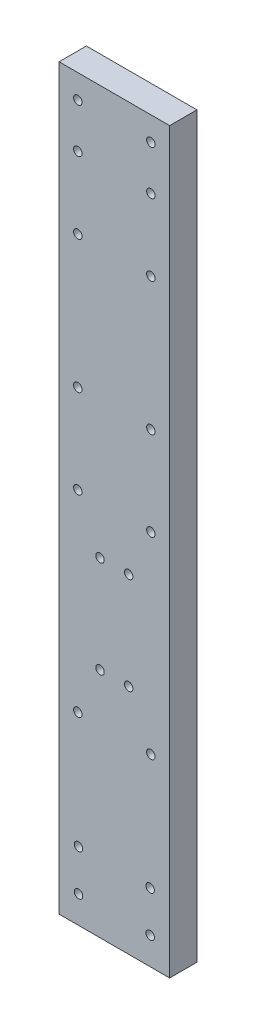
SolidWorks part; units mm, degrees
ref_plane "Front Plane" through (0, 0, 0) normal (0, 0, 1) x (1, 0, 0)
ref_plane "Top Plane" through (0, 0, 0) normal (0, 1, 0) x (1, 0, 0)
ref_plane "Right Plane" through (0, 0, 0) normal (1, 0, 0) x (0, 0, -1)
sketch "Sketch1" plane through (0, 0, 0) normal (0, 0, 1) x (1, 0, 0)
  line L0 (16.2, 0) -> (16.2, 108.14)
  line L1 (16.2, 108.14) -> (0, 108.14)
  line L2 (0, 108.14) -> (0, 0)
  line L3 (0, 0) -> (16.2, 0)
  line L4 (16.2, 57.71) -> (0, 57.71) construction
  line L5 (0, 12.5) -> (16.2, 12.5) construction
  line L6 (0, 24.5) -> (16.2, 24.5) construction
  line L7 (0, 90.16) -> (16.2, 90.16) construction
  line L8 (0, 65.71) -> (16.2, 65.71) construction
  line L9 (8.1, 108.14) -> (8.1, 96.16) construction
  line L11 (0, 96.16) -> (16.2, 96.16) construction
  circle A0 centre (13.45, 55.21) radius 0.62
  circle A1 centre (10.2, 48.21) radius 0.62
  circle A2 centre (13.45, 104.66) radius 0.62
  circle A3 centre (2.75, 98.16) radius 0.62
  circle A4 centre (6, 48.21) radius 0.62
  circle A5 centre (2.75, 27) radius 0.62
  circle A6 centre (2.75, 87.66) radius 0.62
  circle A7 centre (2.75, 55.21) radius 0.62
  circle A8 centre (13.45, 87.66) radius 0.62
  circle A9 centre (13.45, 98.16) radius 0.62
  circle A28 centre (13.45, 68.21) radius 0.62
  circle A29 centre (6, 34) radius 0.62
  circle A32 centre (2.75, 104.66) radius 0.62
  circle A33 centre (10.2, 34) radius 0.62
  circle A34 centre (2.75, 68.21) radius 0.62
  circle A35 centre (13.45, 27) radius 0.62
  circle A36 centre (2.85, 10) radius 0.62
  circle A37 centre (13.35, 10) radius 0.62
  circle A38 centre (13.35, 4) radius 0.62
  circle A39 centre (2.85, 4) radius 0.62
  dimension "D1" = 4
  dimension "D45" = 1.24
  dimension "D2" = 4
  dimension "D3" = 2.85
  dimension "D4" = 2.85
  dimension "D5" = 16.2
  dimension "D6" = 6
  dimension "D7" = 6
  dimension "D8" = 2.85
  dimension "D9" = 2.85
  dimension "D10" = 2.5
  dimension "D11" = 12
  dimension "D12" = 33.21
  dimension "D13" = 2.5
  dimension "D14" = 2.5
  dimension "D15" = 2.75
  dimension "D16" = 2.75
  dimension "D17" = 2.5
  dimension "D18" = 2.5
  dimension "D19" = 2.75
  dimension "D20" = 2.75
  dimension "D21" = 9.5
  dimension "D22" = 6
  dimension "D23" = 9.5
  dimension "D24" = 6
  dimension "D25" = 9.5
  dimension "D26" = 9.5
  dimension "D27" = 6
  dimension "D28" = 6
  dimension "D29" = 8
  dimension "D30" = 24.45
  dimension "D31" = 2.5
  dimension "D32" = 2.5
  dimension "D33" = 2.75
  dimension "D34" = 2.75
  dimension "D35" = 6
  dimension "D36" = 2.75
  dimension "D37" = 2
  dimension "D38" = 2.75
  dimension "D39" = 8.5
  dimension "D40" = 11.98
  dimension "D41" = 2.5
  dimension "D42" = 2.5
  dimension "D43" = 2.75
  dimension "D44" = 2.75
extrude "Boss-Extrude1" add sketch "Sketch1" along normal blind 4
equation "\"D12@Sketch1\"= \"HL@parametersSketch@prostheticParameters.SLDPRT\" * 0.266 - 12 - 4 'Middle PIP Length"
equation "\"D30@Sketch1\"= \"HL@parametersSketch@prostheticParameters.SLDPRT\" * 0.17 - 4 - 3'Middle MIP Length"
equation "\"D5@Sketch1\"= \"fingerWidth@parametersSketch@prostheticParameters.SLDPRT\" 'Middle Width"
equation "\"D40@Sketch1\"= \"HL@parametersSketch@prostheticParameters.SLDPRT\" * 0.108 - 3 - 5'Middle DIP Length"
equation "\"D45@Sketch1\"= 1.04 + \"tol1@parametersSketch@prostheticParameters.SLDPRT\""
